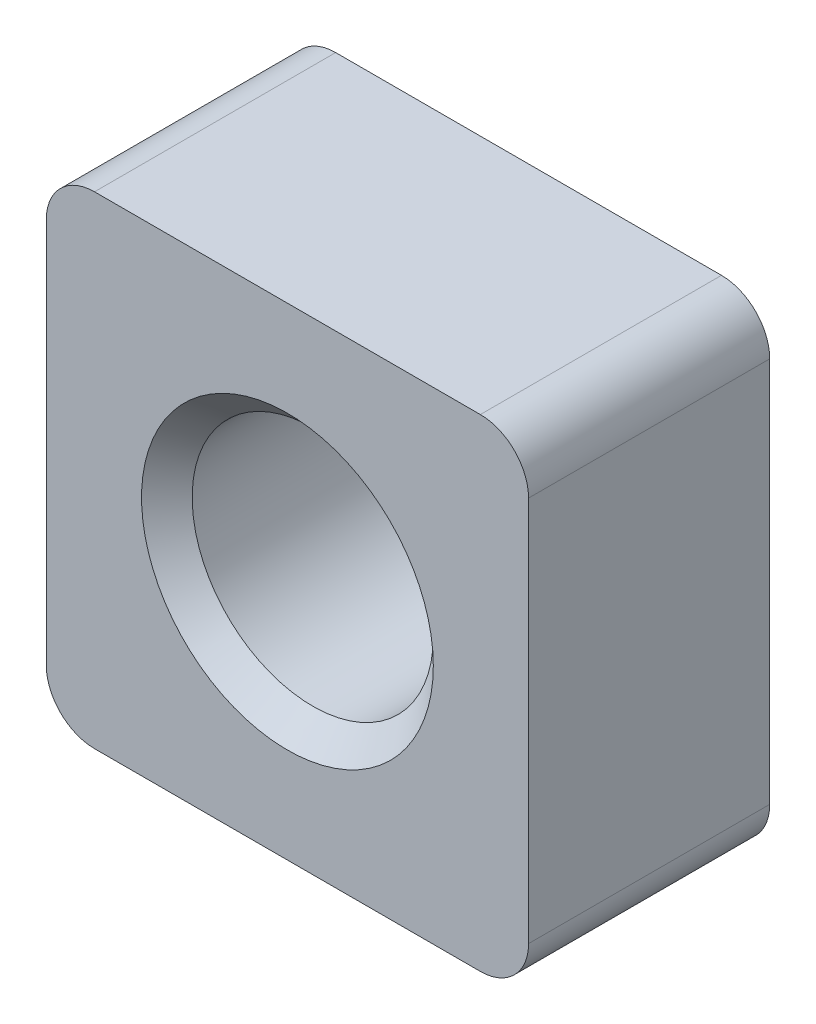
SolidWorks part; units mm, degrees
ref_plane "Спереди" through (0, 0, 0) normal (0, 0, 1) x (1, 0, 0)
ref_plane "Сверху" through (0, 0, 0) normal (0, 1, 0) x (1, 0, 0)
ref_plane "Справа" through (0, 0, 0) normal (1, 0, 0) x (0, 0, -1)
sketch "Эскиз1" plane through (0, 0, 0) normal (0, 0, 1) x (1, 0, 0)
  line L1 (-5, -5) -> (5, -5)
  line L2 (-5, -5) -> (-5, 5)
  line L3 (-5, 5) -> (5, 5)
  line L4 (5, -5) -> (5, 5)
  line L5 (-5, -5) -> (5, 5) construction
  line L6 (-5, 5) -> (5, -5) construction
  point P0 (0, 0)
  dimension "D1" = 10
extrude "Бобышка-Вытянуть1" add sketch "Эскиз1" along normal blind 5
hole_wizard "Отверстие обработанное метчиком M61" positions "Эскиз2" profile "Эскиз3" tap size "M6" standard "ISO" end condition through all
sketch "Эскиз2" plane through (0, 0, 5) normal (0, 0, 1) x (1, 0, 0)
  point P0 (0, 0)
sketch "Эскиз3" plane through (0, 0, 5) normal (1, 0, 0) x (0, -1, 0)
  line L0 (0, 0) -> (0, 5)
  line L1 (0, 5) -> (3.025, 5)
  line L2 (2.5, 4.475) -> (2.5, 0.525)
  line L3 (2.5, 0.525) -> (3.025, 0)
  line L5 (3.025, 0) -> (0, 0)
  line L6 (-2.5, 0.525) -> (-3.025, 0) construction
  line L7 (3.025, 5) -> (2.5, 4.475)
  line L8 (-3.025, 5) -> (-2.5, 4.475) construction
  line L11 (0, -6.35) -> (0, 107.95) construction
  dimension "Диаметр проходного сверла" = 5
  dimension "Глубина проходного сверла" = 5
  dimension "Диаметр передней зенковки" = 6.05
  dimension "Угол передней зенковки" = 90
  dimension "Диаметр задней зенковки" = 6.05
  dimension "Угол задней зенковки" = 90
cosmetic thread "Отверстие резьбы1" parameters "D2"=6
fillet "Скругление1" radius 1 4 edges at (5, 5, 2.5) (-5, 5, 2.5) (5, -5, 2.5) (-5, -5, 2.5)
